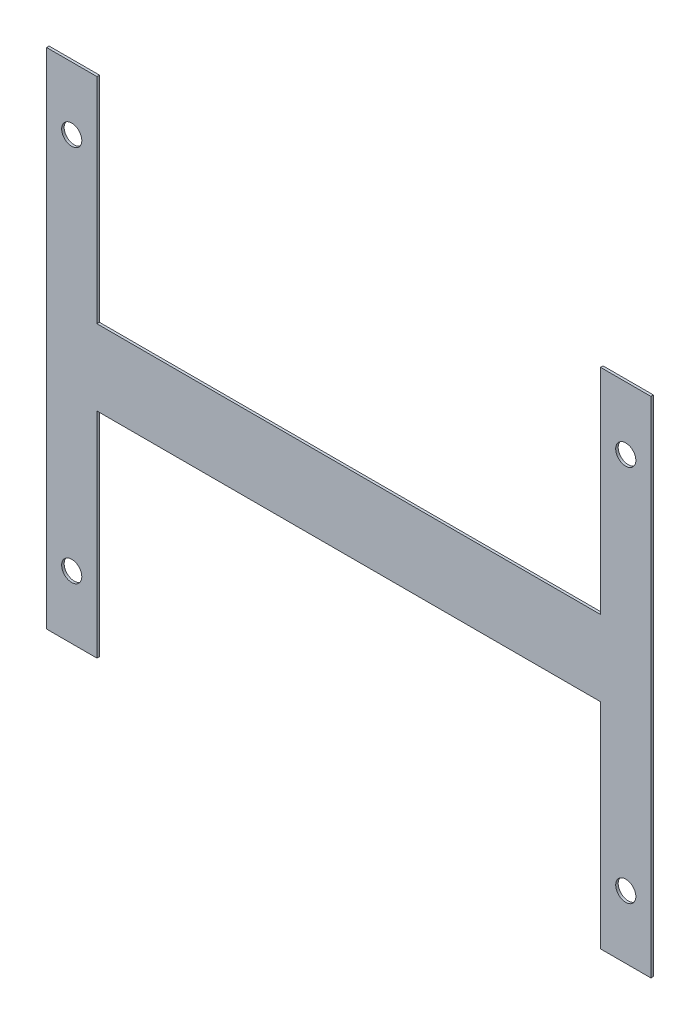
SolidWorks part; units mm, degrees
ref_plane "Front Plane" through (0, 0, 0) normal (0, 0, 1) x (1, 0, 0)
ref_plane "Top Plane" through (0, 0, 0) normal (0, 1, 0) x (1, 0, 0)
ref_plane "Right Plane" through (0, 0, 0) normal (1, 0, 0) x (0, 0, -1)
sketch "Sketch1" plane through (0, 0, 0) normal (0, 0, 1) x (1, 0, 0)
  line L0 (120, 115) -> (120, 85) construction
  line L1 (0, 200) -> (20, 200)
  line L2 (0, 200) -> (0, 0)
  line L3 (0, 0) -> (20, 0)
  line L4 (20, 200) -> (20, 0)
  line L5 (20, 115) -> (220, 115)
  line L6 (20, 115) -> (20, 85)
  line L7 (20, 85) -> (220, 85)
  line L8 (220, 115) -> (220, 85)
  line L13 (240, 0) -> (220, 0)
  line L14 (220, 200) -> (220, 0)
  line L15 (240, 200) -> (220, 200)
  line L16 (240, 200) -> (240, 0)
  line L17 (10, 200) -> (10, 0) construction
  line L18 (0, 100) -> (20, 100) construction
  circle A0 centre (10, 175) radius 4
  circle A1 centre (10, 25) radius 4
  circle A2 centre (230, 25) radius 4
  circle A3 centre (230, 175) radius 4
  dimension "D5" = 8
  dimension "D1" = 200
  dimension "16" = 20
  dimension "D2" = 200
  dimension "D3" = 30
  dimension "D4" = 85
  dimension "D6" = 25
extrude "Boss-Extrude1" add sketch "Sketch1" along normal blind 1 contours L8 L5 L4 L7 | L4 L1 L2 L3 A0 A1 | L16 L15 L14 L8 L13 A2 A3
